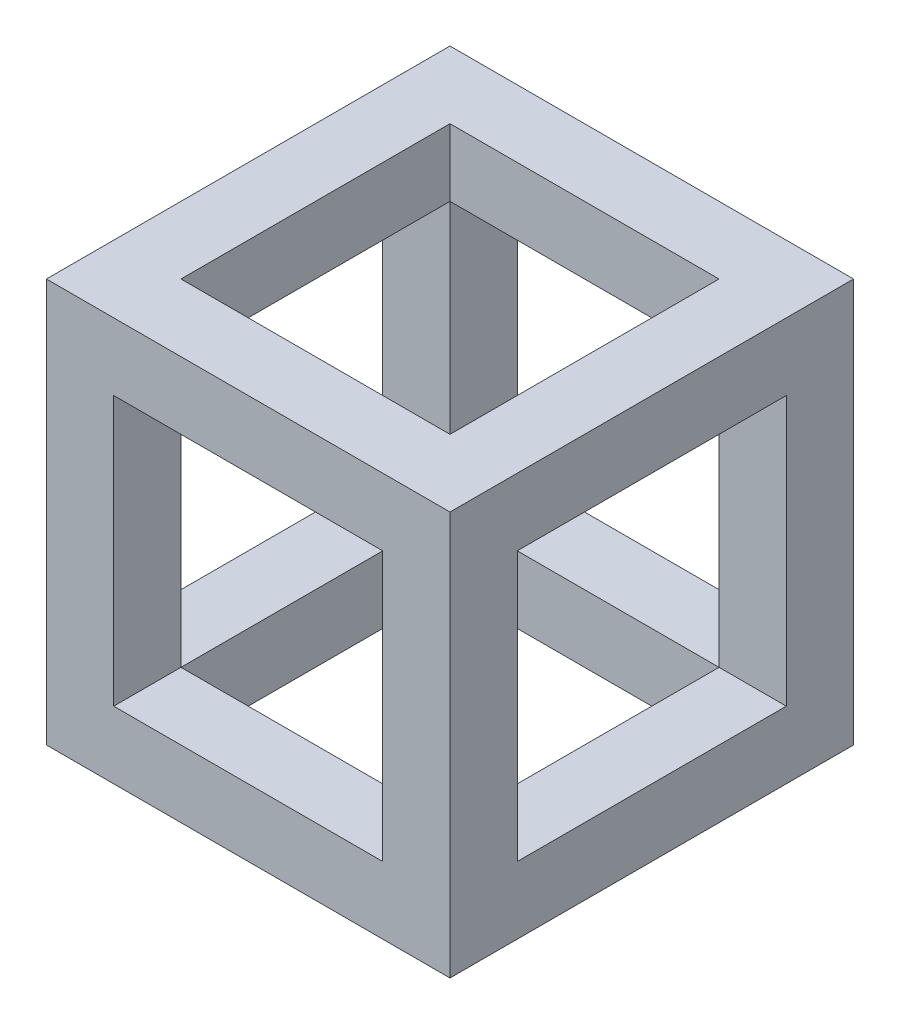
SolidWorks part; units mm, degrees
ref_plane "Plan de face" through (0, 0, 0) normal (0, 0, 1) x (1, 0, 0)
ref_plane "Plan de dessus" through (0, 0, 0) normal (0, 1, 0) x (1, 0, 0)
ref_plane "Plan de droite" through (0, 0, 0) normal (1, 0, 0) x (0, 0, -1)
sketch "Esquisse1" plane through (0, 0, 0) normal (0, 0, 1) x (1, 0, 0)
  line L1 (0, 0) -> (30, 0)
  line L2 (0, 0) -> (0, 30)
  line L3 (0, 30) -> (30, 30)
  line L4 (30, 0) -> (30, 30)
  dimension "D1" = 30
  dimension "D2" = 30
extrude "Boss.-Extru.1" add sketch "Esquisse1" along normal blind 30
sketch "Esquisse2" plane through (0, 30, 0) normal (0, 1, 0) x (1, 0, 0)
  line L0 (0, -30) -> (0, 0) construction
  line L1 (5, -5) -> (25, -5)
  line L2 (5, -5) -> (5, -25)
  line L3 (5, -25) -> (25, -25)
  line L4 (25, -5) -> (25, -25)
  line L5 (30, 0) -> (0, 0) construction
  line L6 (30, -30) -> (30, 0) construction
  line L7 (30, -30) -> (0, -30) construction
  point P4 (0, -15)
  dimension "D1" = 5
  dimension "D2" = 5
  dimension "D3" = 5
  dimension "D4" = 5
extrude "Enlèv. mat.-Extru.1" cut sketch "Esquisse2" against normal through all
sketch "Esquisse3" plane through (0, 0, 30) normal (0, 0, 1) x (1, 0, 0)
  line L0 (30, 30) -> (0, 30) construction
  line L1 (5, 5) -> (25, 5)
  line L2 (5, 5) -> (5, 25)
  line L3 (5, 25) -> (25, 25)
  line L4 (25, 5) -> (25, 25)
  line L5 (0, 30) -> (0, 0) construction
  line L6 (30, 0) -> (30, 30) construction
  line L7 (0, 0) -> (30, 0) construction
  point P6 (0, 15)
  dimension "D1" = 5
  dimension "D2" = 5
  dimension "D3" = 5
  dimension "D4" = 5
extrude "Enlèv. mat.-Extru.2" cut sketch "Esquisse3" against normal through all
sketch "Esquisse4" plane through (30, 0, 0) normal (1, 0, 0) x (0, 0, -1)
  line L0 (-30, 30) -> (0, 30) construction
  line L1 (-25, 5) -> (-5, 5)
  line L2 (-25, 5) -> (-25, 25)
  line L3 (-25, 25) -> (-5, 25)
  line L4 (-5, 5) -> (-5, 25)
  line L5 (0, 0) -> (0, 30) construction
  line L6 (-30, 0) -> (0, 0) construction
  line L7 (-30, 0) -> (-30, 30) construction
  dimension "D1" = 5
  dimension "D2" = 5
  dimension "D3" = 5
  dimension "D4" = 5
extrude "Enlèv. mat.-Extru.3" cut sketch "Esquisse4" against normal through all
